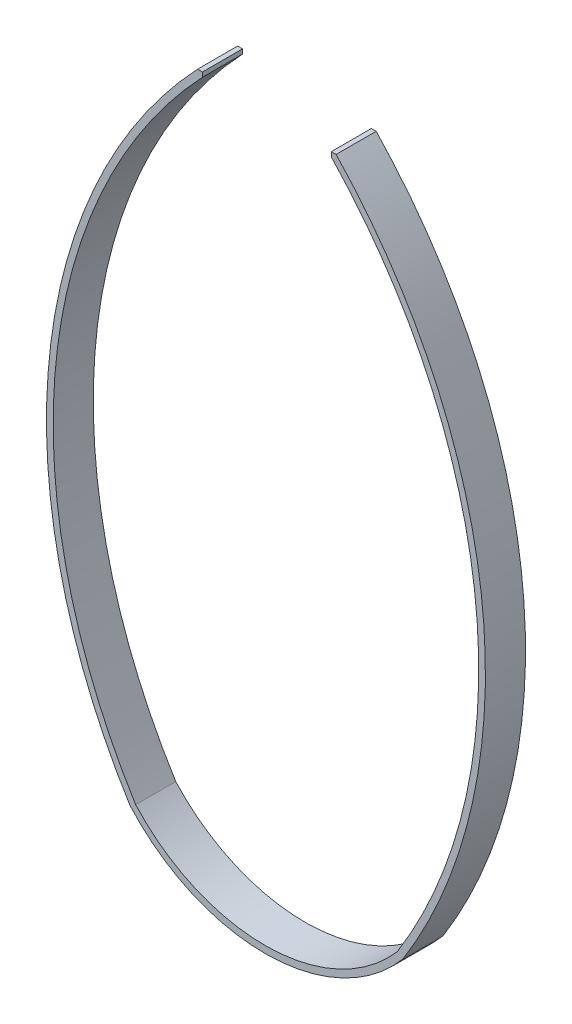
SolidWorks part; units mm, degrees
ref_plane "Plan de face" through (0, 0, 0) normal (0, 0, 1) x (1, 0, 0)
ref_plane "Plan de dessus" through (0, 0, 0) normal (0, 1, 0) x (1, 0, 0)
ref_plane "Plan de droite" through (0, 0, 0) normal (1, 0, 0) x (0, 0, -1)
sketch "Esquisse1" plane through (0, 0, 0) normal (0, 0, 1) x (1, 0, 0)
  line L0 (-50, 263.0077) -> (50, 263.0077) construction
  line L1 (0, 0) -> (0, 109.0003) construction
  line L6 (135.4768, 198.1061) -> (135.4768, -198.1061) construction
  line L7 (-135.4768, 198.1061) -> (-135.4768, -198.1061) construction
  line L12 (46.3684, 259.5708) -> (46.3684, 263.0077)
  line L13 (46.3684, 263.0077) -> (50, 263.0077)
  line L14 (-53.6316, 266.4445) -> (-50, 266.4445)
  line L15 (-50, 266.4445) -> (-50, 263.0077)
  arc A2 (50, 263.0077) -> (99.9773, -233.3633) centre (-246.4467, -17.5416) cw
  arc A3 (99.9773, -233.3633) -> (-104.2211, -236.0071) centre (-3.2655, -146.3567) cw
  arc A4 (-50, 263.0077) -> (-99.9773, -233.3633) centre (246.4467, -17.5416) ccw
  arc A5 (46.3684, 259.5708) -> (95.7335, -230.7194) centre (-246.4467, -17.5416) cw
  arc A6 (-53.6316, 266.4445) -> (-104.2211, -236.0071) centre (246.4467, -17.5416) ccw
  arc A7 (-99.9773, -233.3633) -> (95.7335, -230.7194) centre (-3.2912, -145.4838) ccw
  point P1 (0, 0)
  point P4 (-48.9583, 229.8436)
  point P6 (48.9583, 229.8436)
  dimension "D1" = 100
  dimension "D4" = 5
extrude "Boss.-Extru.1" add sketch "Esquisse1" along normal blind 30
